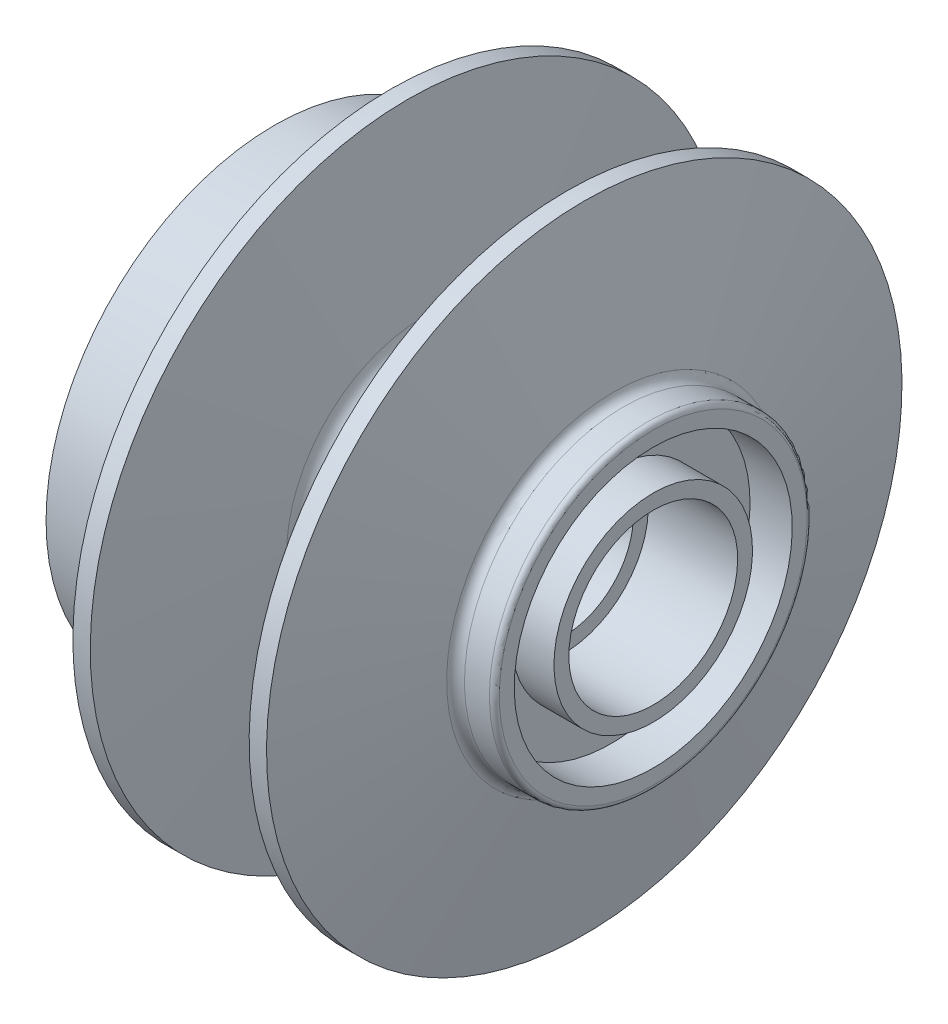
SolidWorks part; units mm, degrees
ref_plane "Front Plane" through (0, 0, 0) normal (0, 0, 1) x (1, 0, 0)
ref_plane "Top Plane" through (0, 0, 0) normal (0, 1, 0) x (1, 0, 0)
ref_plane "Right Plane" through (0, 0, 0) normal (1, 0, 0) x (0, 0, -1)
sketch "Sketch1" plane through (0, 0, 0) normal (0, 0, 1) x (1, 0, 0)
  line L0 (62.0912, 0) -> (-62.0912, 0) construction
  line L1 (-48.1899, 17) -> (-25.1899, 17)
  line L2 (-25.1899, 14) -> (-25.1899, 17)
  line L3 (-25.1899, 14) -> (-4.6899, 14)
  line L4 (-4.1899, 10) -> (-4.1899, 13.5)
  line L5 (-4.1899, 14) -> (-4.1899, 10)
  line L6 (-4.1899, 10) -> (-3.1899, 10)
  line L7 (-3.1899, 10) -> (-3.1899, 13.5)
  line L8 (-2.6899, 14) -> (17.8101, 14)
  line L9 (17.8101, 14) -> (17.8101, 17)
  line L10 (17.8101, 17) -> (35.8101, 17)
  line L11 (-48.1899, 17) -> (-48.1899, 20)
  line L12 (-46.1899, 22) -> (-45.4899, 22)
  line L13 (-44.4899, 23) -> (-44.4899, 28)
  line L14 (-44.4899, 28) -> (-40.4899, 28)
  line L15 (-40.4899, 28) -> (-40.4899, 46)
  line L17 (-18.4168, 48.7607) -> (-17.0835, 64)
  line L18 (-13.5835, 64) -> (-17.0835, 64)
  line L19 (-13.5835, 64) -> (-10.4034, 27.6514)
  line L20 (-6.4187, 24) -> (11.2516, 24)
  line L21 (15.2364, 27.6514) -> (18.4165, 64)
  line L22 (18.4165, 64) -> (21.9165, 64)
  line L23 (21.9165, 64) -> (27.8221, 33.6184)
  line L24 (29.7853, 32) -> (34.8101, 32)
  line L25 (35.8101, 31) -> (35.8101, 28)
  line L26 (35.8101, 28) -> (27.3101, 28)
  line L27 (27.3101, 28) -> (27.3101, 20)
  line L28 (27.3101, 20) -> (35.8101, 20)
  line L29 (35.8101, 20) -> (35.8101, 17)
  line L30 (-40.4899, 46) -> (-19.3258, 47.8516)
  arc A0 (-6.4187, 24) -> (-10.4034, 27.6514) centre (-6.4187, 28) cw
  arc A1 (11.2516, 24) -> (15.2364, 27.6514) centre (11.2516, 28) ccw
  arc A2 (-44.4899, 23) -> (-45.4899, 22) centre (-45.4899, 23) cw
  arc A3 (-46.1899, 22) -> (-48.1899, 20) centre (-46.1899, 20) ccw
  arc A4 (-19.3258, 47.8516) -> (-18.4168, 48.7607) centre (-19.413, 48.8478) ccw
  arc A5 (29.7853, 32) -> (27.8221, 33.6184) centre (29.7853, 34) cw
  arc A6 (35.8101, 31) -> (34.8101, 32) centre (34.8101, 31) ccw
  arc A7 (-4.1899, 13.5) -> (-4.6899, 14) centre (-4.6899, 13.5) ccw
  arc A8 (-2.6899, 14) -> (-3.1899, 13.5) centre (-2.6899, 13.5) ccw
  point P4 (0, 0)
  point P33 (20.1665, 64)
  point P40 (-44.4899, 22)
  point P43 (-48.1899, 22)
  point P46 (-18.4899, 47.9248)
  point P51 (35.8101, 32)
  point P57 (-3.1899, 14)
  dimension "D32" = 4
  dimension "D33" = 4
  dimension "D34" = 1
  dimension "D35" = 2
  dimension "D36" = 1
  dimension "D37" = 2
  dimension "D38" = 1
  dimension "D39" = 0.5
  dimension "D40" = 0.5
  dimension "D1" = 50
  dimension "D2" = 47
  dimension "D3" = 50
  dimension "D4" = 47
  dimension "D5" = 3.5
  dimension "D6" = 3.5
  dimension "D7" = 32
  dimension "D8" = 17
  dimension "D9" = 40
  dimension "D10" = 100
  dimension "D11" = 3
  dimension "D12" = 4
  dimension "D13" = 8
  dimension "D14" = 11
  dimension "D15" = 5
  dimension "D16" = 18
  dimension "D17" = 95
  dimension "D18" = 95
  dimension "D19" = 101
  dimension "D20" = 44
  dimension "D21" = 39
  dimension "D22" = 18
  dimension "D23" = 21
  dimension "D24" = 4
  dimension "D25" = 3.7
  dimension "D26" = 22
  dimension "D27" = 8.5
  dimension "D28" = 8.5
  dimension "D29" = 21
  dimension "D30" = 23
  dimension "D31" = 4
  dimension "D41" = 1
revolve "Revolve3" add sketch "Sketch1" angle 360 about L0
sketch "Sketch2" plane through (-40.4899, 0, 0) normal (-1, 0, 0) x (0, 0, 1)
  line L0 (-38.5576, 6.7987) -> (-36.6005, 6.4537)
  line L5 (-6.7987, 38.5576) -> (-6.4537, 36.6005)
  arc A0 (-9.8607, 30.968) -> (-30.968, 9.8607) centre (0, 0) ccw
  arc A1 (-15.0367, 42.4134) -> (-42.4134, 15.0367) centre (0, 0) ccw
  arc A2 (-30.968, 9.8607) -> (-36.6005, 6.4537) centre (-35.7323, 11.3777) cw
  arc A3 (-9.8607, 30.968) -> (-6.4537, 36.6005) centre (-11.3777, 35.7323) ccw
  arc A8 (-38.5576, 6.7987) -> (-42.4134, 15.0367) centre (-42.7439, 9.8607) ccw
  arc A9 (-6.7987, 38.5576) -> (-15.0367, 42.4134) centre (-9.8607, 42.7439) cw
  dimension "D1" = 65
  dimension "D2" = 90
  dimension "D3" = 5
  dimension "D4" = 5
extrude "Cut-Extrude1" cut sketch "Sketch2" against normal blind 20
